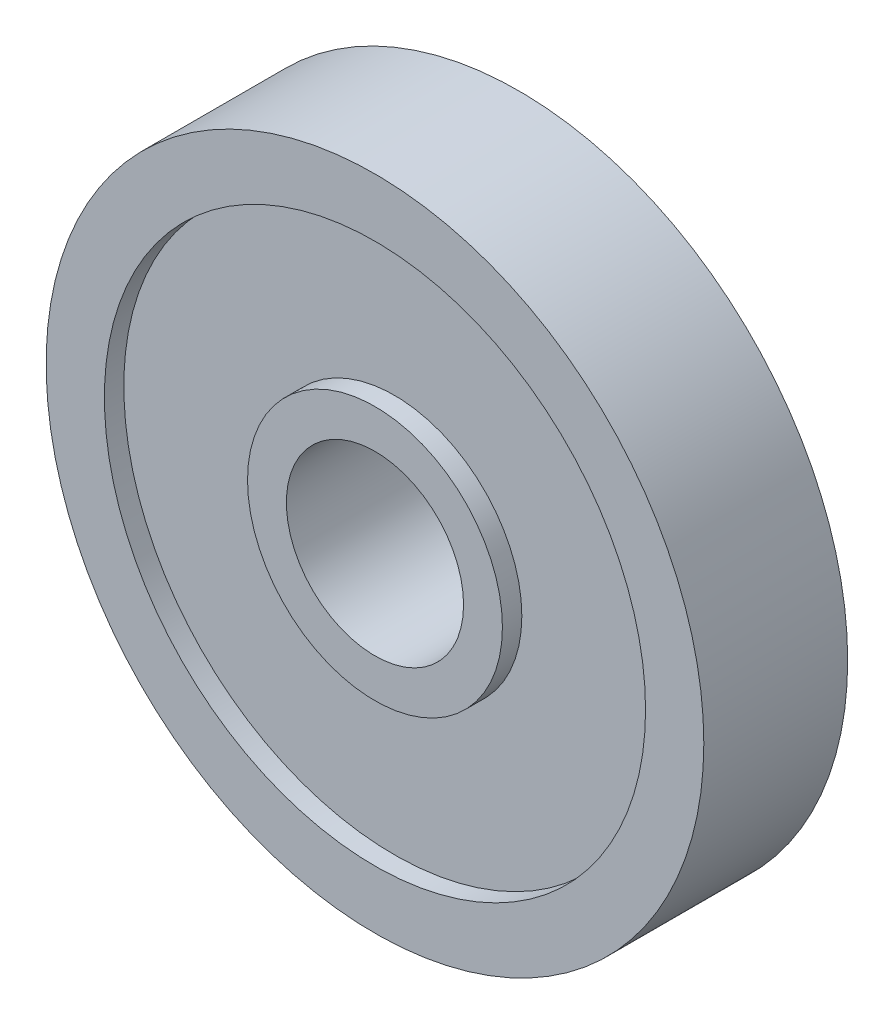
SolidWorks part; units mm, degrees
ref_plane "Front Plane" through (0, 0, 0) normal (0, 0, 1) x (1, 0, 0)
ref_plane "Top Plane" through (0, 0, 0) normal (0, 1, 0) x (1, 0, 0)
ref_plane "Right Plane" through (0, 0, 0) normal (1, 0, 0) x (0, 0, -1)
sketch "Sketch1" plane through (0, 0, 0) normal (0, 0, 1) x (1, 0, 0)
  circle A0 centre (-108.0429, 14.6365) radius 16.9333
  circle A4 centre (-108.0429, 14.6365) radius 4.5625
  dimension "D1" = 33.8667
extrude "Boss-Extrude1" add sketch "Sketch1" along normal blind 7.4083
sketch "Sketch2" plane through (0, 0, 7.4083) normal (0, 0, 1) x (1, 0, 0)
  circle A2 centre (-108.0429, 14.6365) radius 13.9333
  circle A3 centre (-108.0429, 14.6365) radius 13.9333
  circle A5 centre (-108.0429, 14.6365) radius 6.5625
  circle A6 centre (-108.0429, 14.6365) radius 6.5625
  dimension "D1" = 3
  dimension "D2" = 2
extrude "Cut-Extrude1" cut sketch "Sketch2" against normal blind 1
ref_plane "Plane1" through (0, 0, 3.7042) normal (0, 0, 1) x (1, 0, 0)
mirror "Mirror1" about plane through (0, 0, 3.7042) normal (0, 0, 1) of "Cut-Extrude1"
